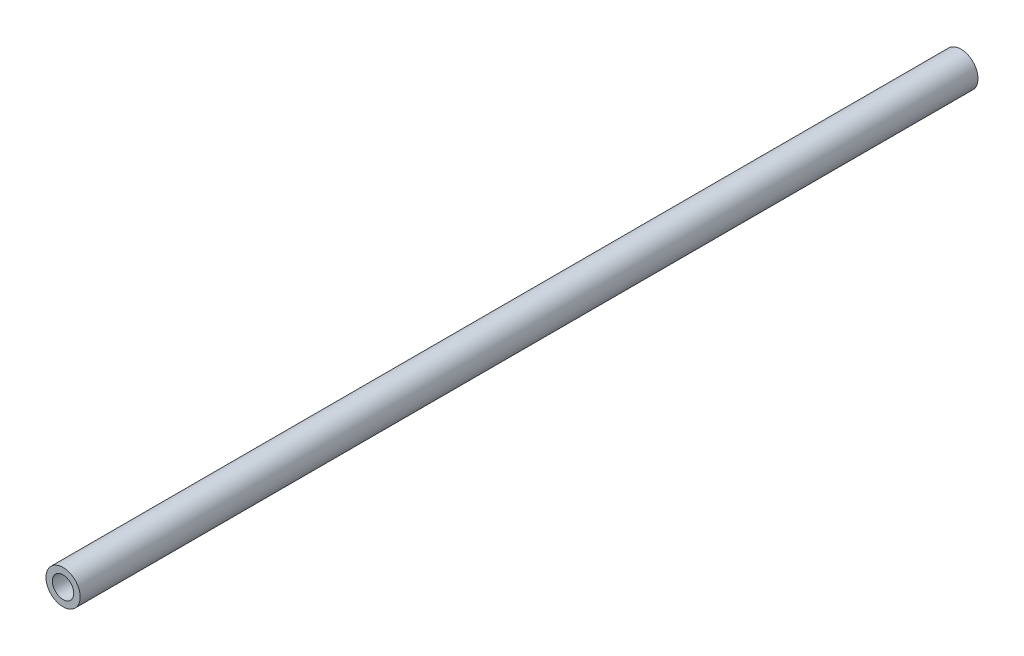
SolidWorks part; units mm, degrees
ref_plane "Front" through (0, 0, 0) normal (0, 0, 1) x (1, 0, 0)
ref_plane "Top" through (0, 0, 0) normal (0, 1, 0) x (1, 0, 0)
ref_plane "Right" through (0, 0, 0) normal (1, 0, 0) x (0, 0, -1)
sketch "草图1" plane through (0, 0, 0) normal (0, 0, 1) x (1, 0, 0)
  circle A0 centre (0, 0) radius 2.5
  circle A1 centre (0, 0) radius 4
extrude "凸台-拉伸1" add sketch "草图1" along normal blind 210
